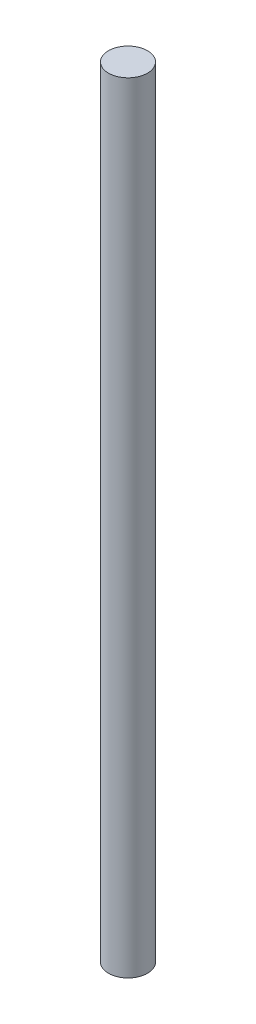
SolidWorks part; units mm, degrees
ref_plane "Front Plane" through (0, 0, 0) normal (0, 0, 1) x (1, 0, 0)
ref_plane "Top Plane" through (0, 0, 0) normal (0, 1, 0) x (1, 0, 0)
ref_plane "Right Plane" through (0, 0, 0) normal (1, 0, 0) x (0, 0, -1)
sketch "Sketch1" plane through (0, 0, 0) normal (0, 1, 0) x (1, 0, 0)
  circle A0 centre (0, 0) radius 0.125
  dimension "D1" = 0.25
extrude "Boss-Extrude1" add sketch "Sketch1" along normal blind 5
